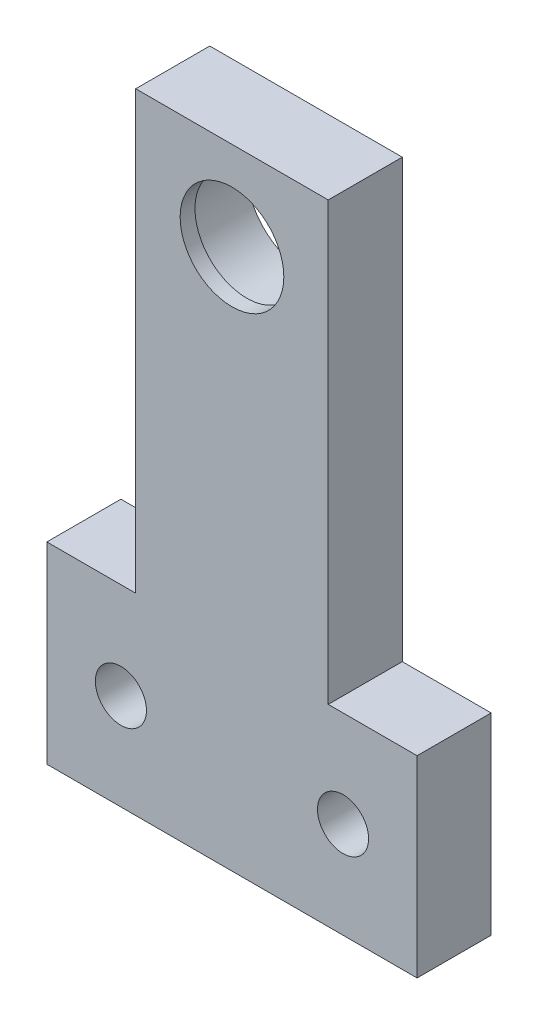
SolidWorks part; units mm, degrees
material "6061 合金"
ref_plane "前视基准面" through (0, 0, 0) normal (0, 0, 1) x (1, 0, 0)
ref_plane "上视基准面" through (0, 0, 0) normal (0, 1, 0) x (1, 0, 0)
ref_plane "右视基准面" through (0, 0, 0) normal (1, 0, 0) x (0, 0, -1)
sketch "草图1" plane through (0, 0, 0) normal (0, 0, 1) x (1, 0, 0)
  line L0 (-25, 0) -> (25, 0)
  line L1 (25, 0) -> (25, 26)
  line L2 (25, 26) -> (13, 26)
  line L3 (13, 26) -> (13, 85)
  line L4 (13, 85) -> (-13, 85)
  line L5 (-13, 85) -> (-13, 26)
  line L6 (-13, 26) -> (-25, 26)
  line L7 (-25, 26) -> (-25, 0)
  line L8 (0, -30.1401) -> (0, 136.3287) construction
  line L9 (-91.0979, 13) -> (78.0415, 13) construction
  circle A0 centre (0, 73) radius 7
  circle A3 centre (-15, 13) radius 3.45
  circle A6 centre (15, 13) radius 3.45
  dimension "D5" = 6.9
  dimension "D6" = 12
  dimension "D8" = 10
  dimension "D9" = 14
  dimension "D1" = 50
  dimension "D2" = 85
  dimension "D3" = 26
  dimension "D4" = 26
extrude "凸台-拉伸1" add sketch "草图1" along normal blind 10
sketch "草图2" plane through (0, 0, 0) normal (0, 0, -1) x (-1, 0, 0)
  circle A0 centre (0, 73) radius 4
  circle A1 centre (0, 73) radius 8.05
  dimension "D1" = 8
  dimension "D2" = 16.1
extrude "切除-拉伸1" cut sketch "草图2" against normal blind 8
